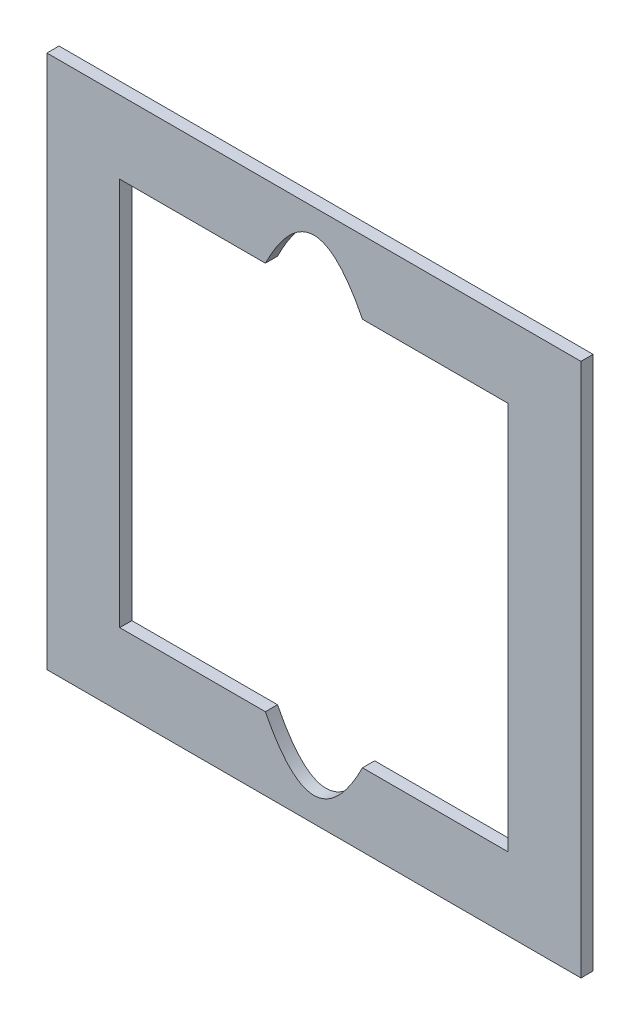
SolidWorks part; units mm, degrees
ref_plane "Front Plane" through (0, 0, 0) normal (0, 0, 1) x (1, 0, 0)
ref_plane "Top Plane" through (0, 0, 0) normal (0, 1, 0) x (1, 0, 0)
ref_plane "Right Plane" through (0, 0, 0) normal (1, 0, 0) x (0, 0, -1)
sketch "Sketch1" plane through (0, 0, 0) normal (0, 0, 1) x (1, 0, 0)
  line L0 (19.05, 120.65) -> (57.15, 120.65)
  line L1 (0, 0) -> (139.7, 0)
  line L2 (0, 0) -> (0, 139.7)
  line L3 (0, 139.7) -> (139.7, 139.7)
  line L4 (139.7, 0) -> (139.7, 139.7)
  line L5 (82.55, 120.65) -> (120.65, 120.65)
  line L6 (19.05, 120.65) -> (19.05, 19.05)
  line L7 (19.05, 19.05) -> (57.15, 19.05)
  line L8 (120.65, 120.65) -> (120.65, 19.05)
  line L9 (82.55, 19.05) -> (120.65, 19.05)
  spline S0 degree 2 poles (57.15, 120.65) (69.85, 146.05) (82.55, 120.65) knots 0 0 0 1 1 1
  spline S1 degree 2 poles (57.15, 19.05) (69.85, -6.1554) (82.55, 19.05) knots 0 0 0 1 1 1
extrude "Boss-Extrude1" add sketch "Sketch1" along normal blind 3.175
